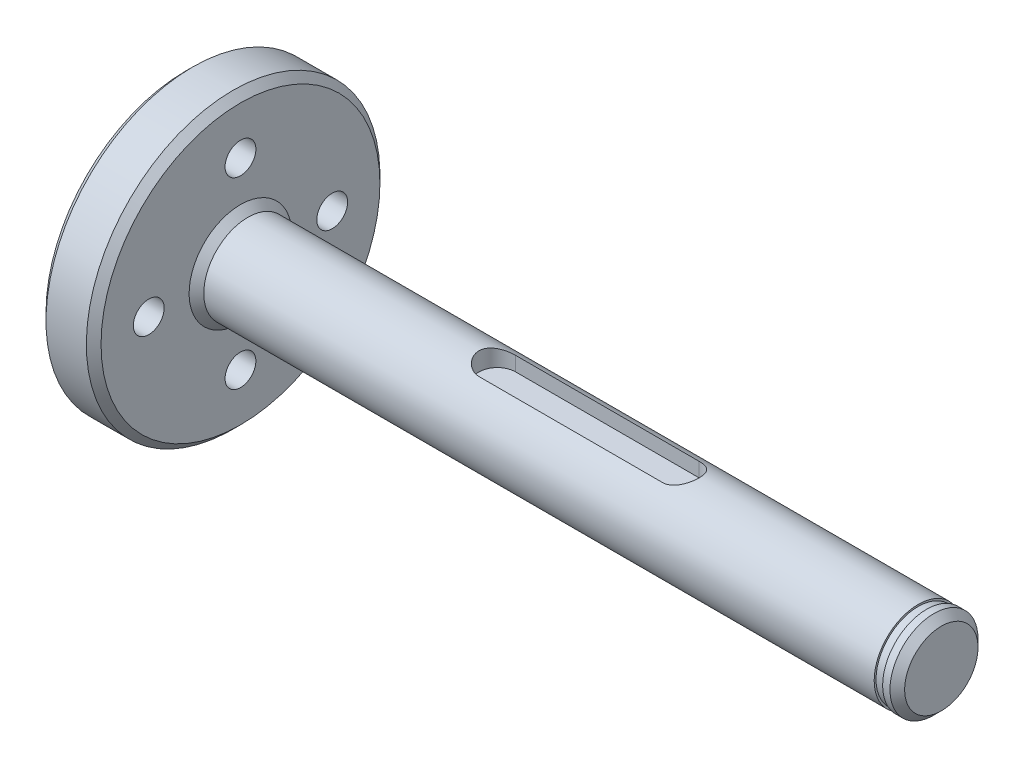
SolidWorks part; units mm, degrees
material "Chrome Stainless Steel"
ref_plane "Front Plane" through (0, 0, 0) normal (0, 0, 1) x (1, 0, 0)
ref_plane "Top Plane" through (0, 0, 0) normal (0, 1, 0) x (1, 0, 0)
ref_plane "Right Plane" through (0, 0, 0) normal (1, 0, 0) x (0, 0, -1)
sketch "Sketch1" plane through (0, 0, 0) normal (0, 0, 1) x (1, 0, 0)
  line L0 (0, 0) -> (0, 20)
  line L1 (0, 20) -> (7.5, 20)
  line L2 (7.5, 20) -> (7.5, 6)
  line L3 (7.5, 6) -> (103, 6)
  line L4 (103, 6) -> (103, 0)
  line L5 (103, 0) -> (0, 0) construction
  line L6 (0, 0) -> (103, 0)
  dimension "D1" = 7.5
  dimension "D2" = 12
  dimension "D3" = 40
  dimension "D4" = 103
revolve "Revolve1" add sketch "Sketch1" angle 360 about L5
chamfer "Chamfer1" distance 1 angle 45 4 edges at (0, 20, 0) (7.5, 20, 0) (103, 6, 0) (7.5, 6, 0)
hole_wizard "M5 Tapped Hole1" positions "Sketch3" profile "Sketch4" tap size "M5" standard "DIN" end condition through all
sketch "Sketch3" plane through (0, 0, 0) normal (-1, 0, 0) x (0, 0, 1)
  line L0 (0, 12.5) -> (0, -12.5) construction
  circle A0 centre (0, 0) radius 12.5 construction
  point P5 (0, 12.5)
  point P14 (12.5, 0)
  point P15 (0, -12.5)
  point P16 (-12.5, 0)
  dimension "D1" = 25
  dimension "D2" = 4
sketch "Sketch4" plane through (0, 0, -12.5) normal (0, 1, 0) x (0, 0, 1)
  line L0 (0, 0) -> (0, 103)
  line L1 (0, 103) -> (2.1, 103)
  line L2 (2.1, 103) -> (2.1, 0)
  line L5 (2.1, 0) -> (0, 0)
  line L11 (0, -6.35) -> (0, 107.95) construction
  dimension "Thru Tap Drill Dia." = 4.2
  dimension "Thru Tap Drill Depth" = 103
cosmetic thread "Hole Thread1" parameters "D2"=5
cosmetic thread "Hole Thread2" parameters "D2"=5
cosmetic thread "Hole Thread3" parameters "D2"=5
cosmetic thread "Hole Thread4" parameters "D2"=5
ref_plane "Plane1" through (0, 6, 0) normal (0, 1, 0) x (1, 0, 0)
sketch "Sketch5" plane through (0, 6, 0) normal (0, 1, 0) x (1, 0, 0)
  line L0 (42.5, 0) -> (67.5, 0) construction
  line L1 (42.5, 2.5) -> (67.5, 2.5)
  line L2 (42.5, -2.5) -> (67.5, -2.5)
  arc A0 (42.5, 2.5) -> (42.5, -2.5) centre (42.5, 0) ccw
  arc A1 (67.5, -2.5) -> (67.5, 2.5) centre (67.5, 0) ccw
  point P3 (55, 0)
  point P8 (40, 0)
  point P9 (70, 0)
  dimension "D1" = 5
  dimension "D2" = 30
  dimension "D3" = 40
extrude "Cut-Extrude1" cut sketch "Sketch5" against normal blind 2.5
sketch "Sketch6" plane through (0, 0, 0) normal (0, 1, 0) x (1, 0, 0)
  line L0 (0, 0) -> (103, 0) construction
  line L1 (103, -5) -> (103, 5) construction
  line L2 (102, 6) -> (8.5, 6) construction
  line L3 (99.85, 6) -> (101, 6)
  line L4 (99.85, 6) -> (99.85, 5.75)
  line L5 (99.85, 5.75) -> (101, 5.75)
  line L6 (101, 6) -> (101, 5.75)
  dimension "D1" = 11.5
  dimension "D2" = 1.15
  dimension "D3" = 2
revolve "Cut-Revolve1" cut sketch "Sketch6" angle 360 about L0
